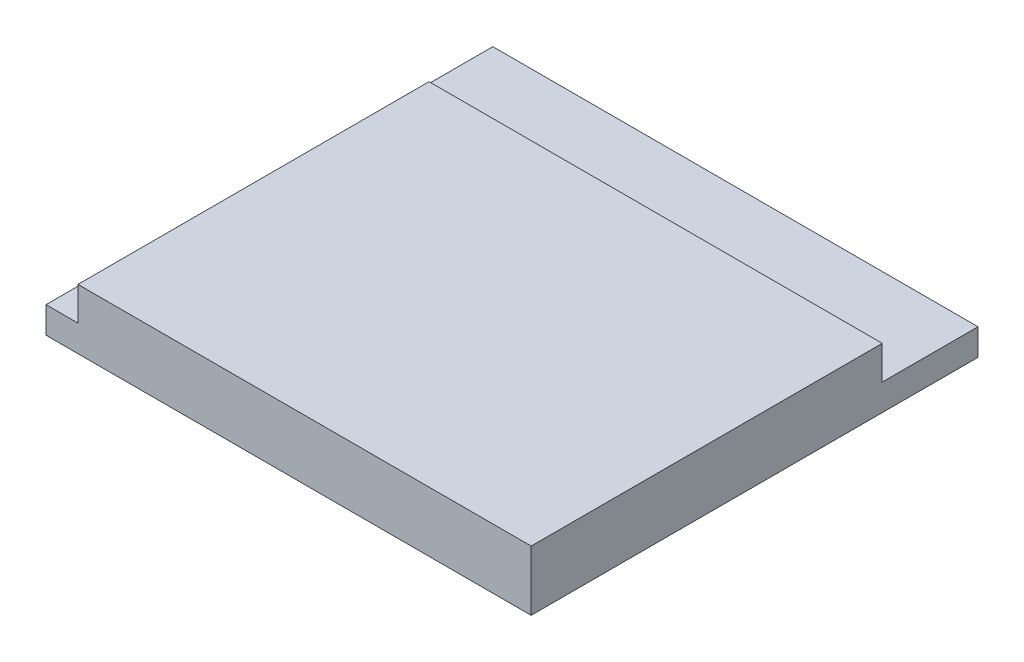
SolidWorks part; units mm, degrees
material "Custom Plastic"
ref_plane "Front Plane" through (0, 0, 0) normal (0, 0, 1) x (1, 0, 0)
ref_plane "Top Plane" through (0, 0, 0) normal (0, 1, 0) x (1, 0, 0)
ref_plane "Right Plane" through (0, 0, 0) normal (1, 0, 0) x (0, 0, -1)
sketch "Sketch1" plane through (0, 0, 0) normal (0, 1, 0) x (1, 0, 0)
  line L1 (-7.6, 7) -> (7.6, 7)
  line L2 (-7.6, 7) -> (-7.6, -7)
  line L3 (-7.6, -7) -> (7.6, -7)
  line L4 (7.6, 7) -> (7.6, -7)
  line L5 (-7.6, 7) -> (7.6, -7) construction
  line L6 (-7.6, -7) -> (7.6, 7) construction
  point P0 (0, 0)
  dimension "D1" = 14
  dimension "D2" = 15.2
extrude "Boss-Extrude1" add sketch "Sketch1" along normal blind 0.83
sketch "Sketch2" plane through (0, 0.83, 0) normal (0, 1, 0) x (1, 0, 0)
  line L1 (7.6, -7) -> (-6.6, -7)
  line L2 (7.6, -7) -> (7.6, 4)
  line L3 (7.6, 4) -> (-6.6, 4)
  line L4 (-6.6, -7) -> (-6.6, 4)
  dimension "D1" = 11
  dimension "D2" = 14.2
extrude "Boss-Extrude2" add sketch "Sketch2" along normal blind 1.05
